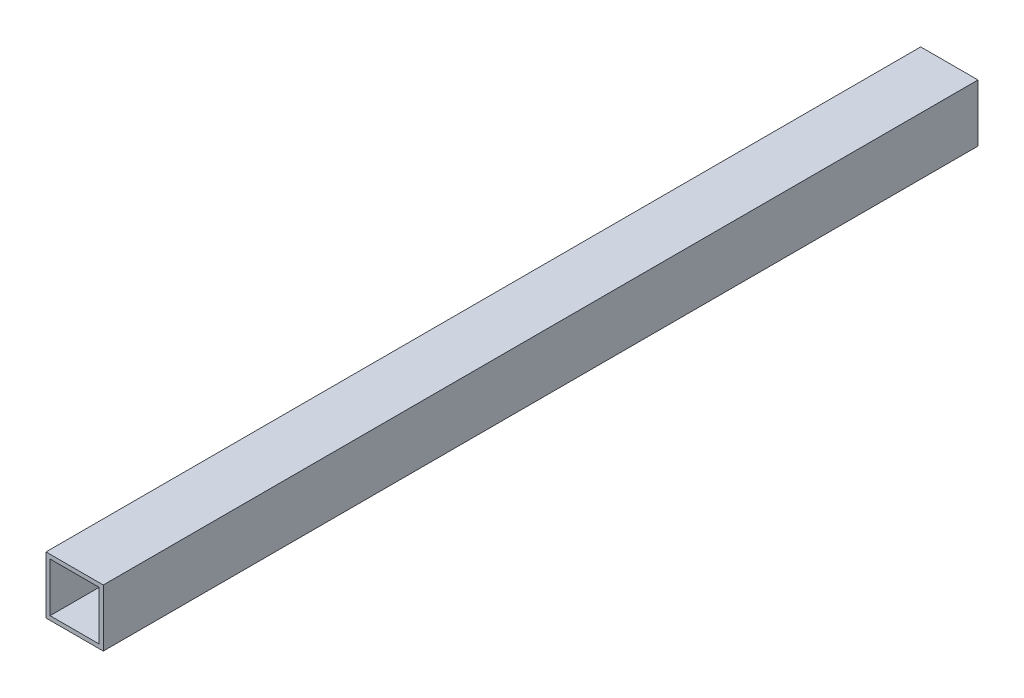
SolidWorks part; units mm, degrees
material "6061 Alloy"
ref_plane "Front Plane" through (0, 0, 0) normal (0, 0, 1) x (1, 0, 0)
ref_plane "Top Plane" through (0, 0, 0) normal (0, 1, 0) x (1, 0, 0)
ref_plane "Right Plane" through (0, 0, 0) normal (1, 0, 0) x (0, 0, -1)
sketch "Sketch1" plane through (0, 0, 0) normal (0, 0, 1) x (1, 0, 0)
  line L0 (-19.05, -19.05) -> (-19.05, 19.05)
  line L1 (-22.225, -22.225) -> (22.225, -22.225)
  line L2 (-22.225, -22.225) -> (-22.225, 22.225)
  line L3 (-22.225, 22.225) -> (22.225, 22.225)
  line L4 (22.225, -22.225) -> (22.225, 22.225)
  line L5 (-22.225, -22.225) -> (22.225, 22.225) construction
  line L6 (-22.225, 22.225) -> (22.225, -22.225) construction
  line L7 (-19.05, 19.05) -> (19.05, 19.05)
  line L8 (19.05, -19.05) -> (19.05, 19.05)
  line L9 (-19.05, -19.05) -> (19.05, -19.05)
  point P0 (0, 0)
  dimension "D1" = 44.45
  dimension "D2" = 44.45
  dimension "D3" = 3.175
extrude "Boss-Extrude1" add sketch "Sketch1" along normal blind 678.815
hole_wizard "J (0.277) Diameter Hole1" positions "3DSketch2" profile "Sketch4" hole size "J" standard "ANSI Inch"
sketch3d "3DSketch2"
  line L0 (-22.225, 22.225, 0) -> (-22.225, -22.225, 0) construction
  line L1 (-22.225, 22.225, 678.815) -> (-22.225, 22.225, 0) construction
  line L2 (-22.225, 22.225, 678.815) -> (-22.225, -22.225, 678.815) construction
  point P0 (-22.225, 0, 338.7427)
  point P2 (-22.225, -0.127, 653.415)
  point P4 (-22.225, 0, 25.4)
  dimension "D1" = 25.4
  dimension "D2" = 22.225
  dimension "D3" = 22.225
  dimension "D4" = 339.471
  dimension "D5" = 22.352
  dimension "D6" = 25.4
sketch "Sketch4" plane through (-22.225, 0, 338.7427) normal (0, 1, 0) x (0, 0, 1)
  line L0 (0, 0) -> (0, 44.45)
  line L1 (0, 44.45) -> (3.5179, 44.45)
  line L2 (3.5179, 44.45) -> (3.5179, 0)
  line L5 (3.5179, 0) -> (0, 0)
  line L11 (0, -6.35) -> (0, 107.95) construction
  dimension "Thru Hole Dia." = 7.0358
  dimension "Thru Hole Depth" = 44.45
